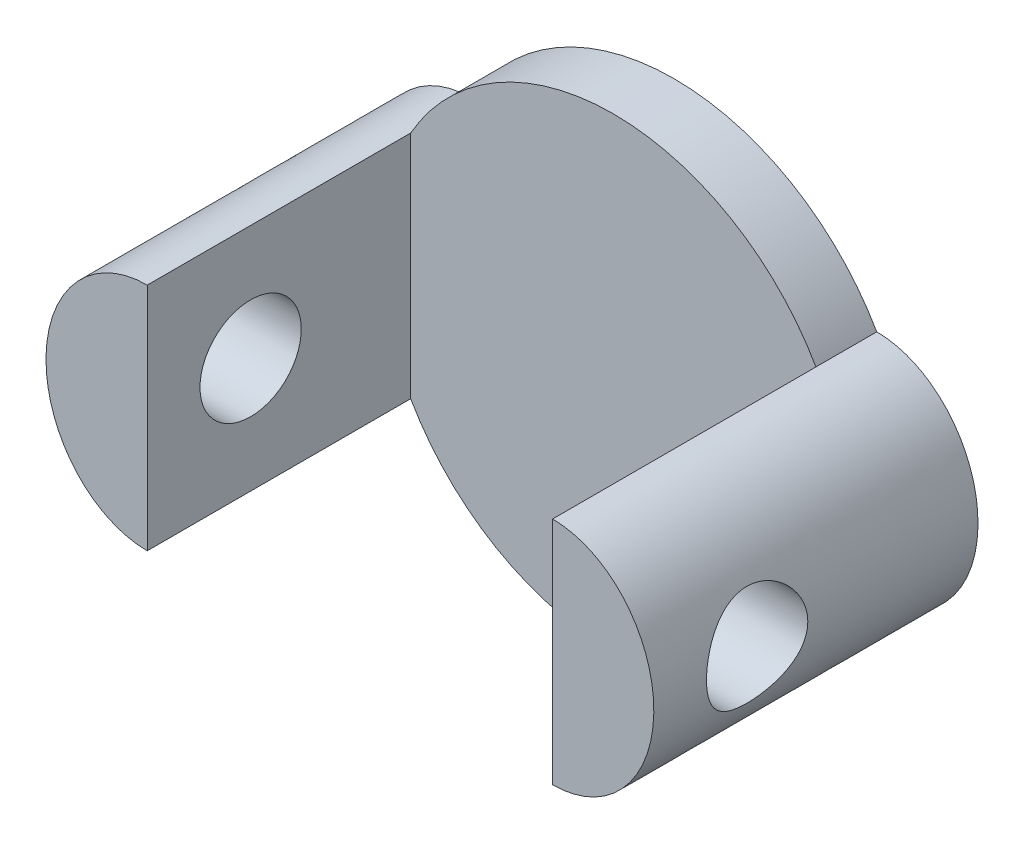
SolidWorks part; units mm, degrees
ref_plane "Front Plane" through (0, 0, 0) normal (0, 0, 1) x (1, 0, 0)
ref_plane "Top Plane" through (0, 0, 0) normal (0, 1, 0) x (1, 0, 0)
ref_plane "Right Plane" through (0, 0, 0) normal (1, 0, 0) x (0, 0, -1)
sketch "Sketch1" plane through (0, 0, 0) normal (0, 0, 1) x (1, 0, 0)
  line L0 (0, 115) -> (0, -115) construction
  arc A0 (-100, -56.7891) -> (100, -56.7891) centre (0, 0) ccw
  arc A1 (100, 56.7891) -> (-100, 56.7891) centre (0, 0) ccw
  ellipse E0 centre (-100, 0) end of major axis (-100, -56.7891) minor radius 50 (-100, 56.7891) -> (-100, -56.7891) ccw
  ellipse E1 centre (100, 0) end of major axis (100, 56.7891) minor radius 50 (100, 56.7891) -> (100, -56.7891) cw
  dimension "D1" = 230
  dimension "D2" = 50
  dimension "D3" = 100
extrude "Boss-Extrude1" add sketch "Sketch1" along normal blind 160
sketch "Sketch3" plane through (0, 0, 160) normal (0, 0, 1) x (1, 0, 0)
  line L1 (-100, 123.6122) -> (100, 123.6122)
  line L2 (-100, 123.6122) -> (-100, -123.6122)
  line L3 (-100, -123.6122) -> (100, -123.6122)
  line L4 (100, 123.6122) -> (100, -123.6122)
extrude "Cut-Extrude1" cut sketch "Sketch3" against normal blind 130
sketch "Sketch4" plane through (-100, 0, 0) normal (1, 0, 0) x (0, 0, -1)
  line L0 (0, -56.7891) -> (0, 56.7891) construction
  circle A0 centre (-109, 0) radius 25
  point P4 (0, 0)
  dimension "D2" = 50
  dimension "D1" = 109
extrude "Cut-Extrude2" cut sketch "Sketch4" against normal through all and the other way through all
